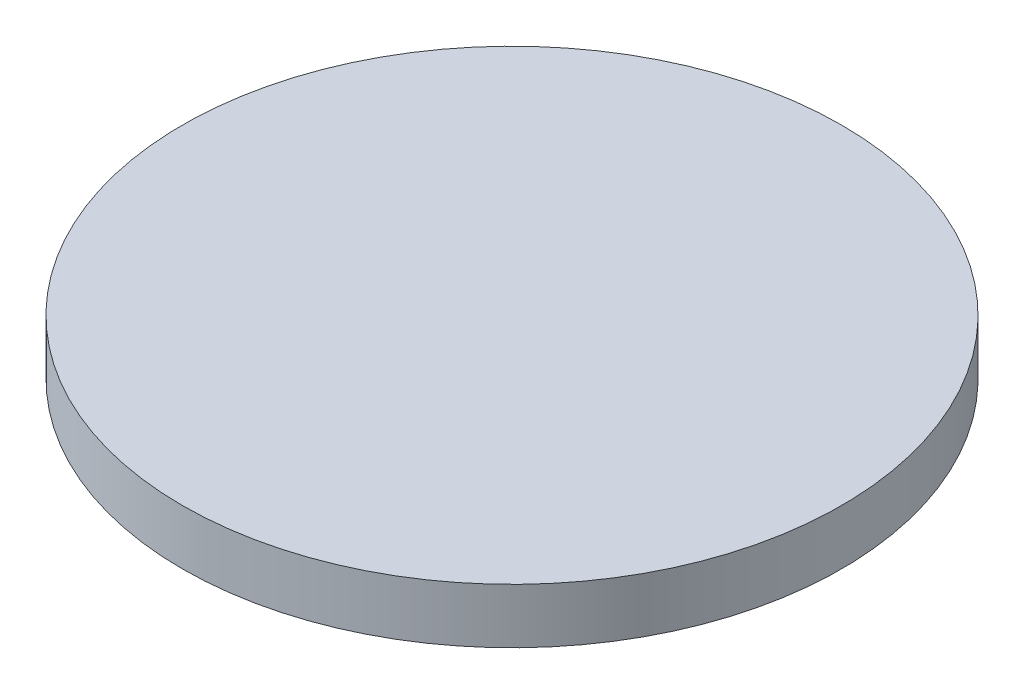
SolidWorks part; units mm, degrees
material "Silicon Rubber"
ref_plane "Front Plane" through (0, 0, 0) normal (0, 0, 1) x (1, 0, 0)
ref_plane "Top Plane" through (0, 0, 0) normal (0, 1, 0) x (1, 0, 0)
ref_plane "Right Plane" through (0, 0, 0) normal (1, 0, 0) x (0, 0, -1)
sketch "Sketch1" plane through (0, 0, 0) normal (0, 1, 0) x (1, 0, 0)
  circle A0 centre (0, 0) radius 6
  dimension "D1" = 12
extrude "Boss-Extrude1" add sketch "Sketch1" along normal blind 1
